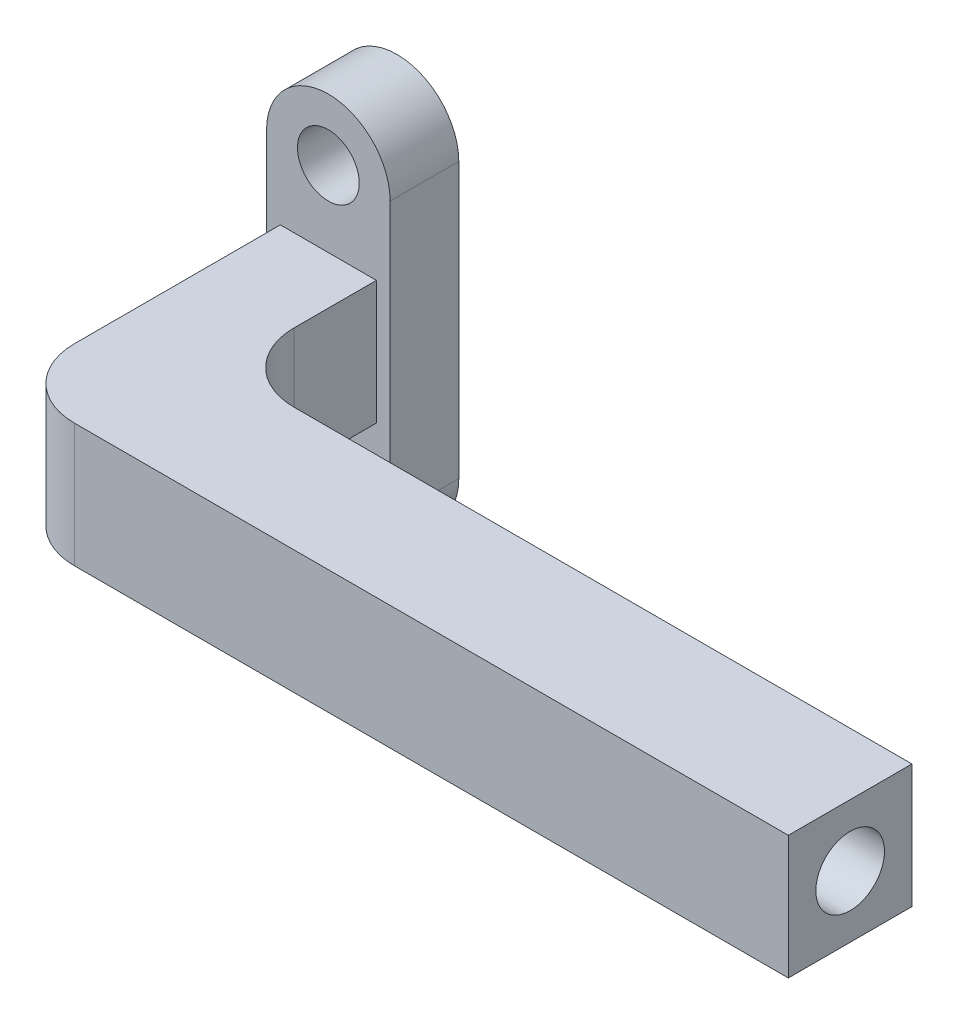
SolidWorks part; units mm, degrees
ref_plane "Front Plane" through (0, 0, 0) normal (0, 0, 1) x (1, 0, 0)
ref_plane "Top Plane" through (0, 0, 0) normal (0, 1, 0) x (1, 0, 0)
ref_plane "Right Plane" through (0, 0, 0) normal (1, 0, 0) x (0, 0, -1)
sketch "Sketch1" plane through (0, 0, 0) normal (0, 0, 1) x (1, 0, 0)
  line L0 (4.5, 10) -> (4.5, -10)
  line L1 (-4.5, 10) -> (-4.5, -10)
  circle A0 centre (0, 10) radius 2.25
  circle A1 centre (0, -10) radius 2.25
  circle A2 centre (0, 10) radius 4.5
  circle A3 centre (0, -10) radius 4.5
  dimension "D1" = 4.5
  dimension "D2" = 9
  dimension "D3" = 4.5
  dimension "D4" = 9
  dimension "D5" = 20
  dimension "D6" = 10
extrude "Boss-Extrude1" add sketch "Sketch1" along normal blind 5 contours A3 L0 A2 L1 | A3 A1 | A0
sketch "Sketch2" plane through (0, 0, 5) normal (0, 0, 1) x (1, 0, 0)
  line L1 (-3.5, -4.5) -> (3.5, -4.5)
  line L2 (-3.5, -4.5) -> (-3.5, 4.5)
  line L3 (-3.5, 4.5) -> (3.5, 4.5)
  line L4 (3.5, -4.5) -> (3.5, 4.5)
  line L5 (-3.5, -4.5) -> (3.5, 4.5) construction
  line L6 (-3.5, 4.5) -> (3.5, -4.5) construction
  point P0 (0, 0)
  dimension "D1" = 9
  dimension "D2" = 7
extrude "Boss-Extrude2" add sketch "Sketch2" along normal blind 20
sketch "Sketch4" plane through (3.5, 0, 0) normal (1, 0, 0) x (0, 0, -1)
  line L0 (-25, -4.5) -> (-5, -4.5) construction
  line L1 (-25, 4.5) -> (-16, 4.5)
  line L2 (-25, 4.5) -> (-25, -4.5)
  line L3 (-25, -4.5) -> (-16, -4.5)
  line L4 (-16, 4.5) -> (-16, -4.5)
  dimension "D1" = 9
extrude "Boss-Extrude4" add sketch "Sketch4" along normal blind 50
sketch "Sketch5" plane through (53.5, 0, 0) normal (1, 0, 0) x (0, 0, -1)
  circle A0 centre (-20.5, 0) radius 2.5
  dimension "D1" = 5
extrude "Cut-Extrude1" cut sketch "Sketch5" against normal blind 25
fillet "Fillet1" radius 5 1 edges at (3.5, 0, 16)
fillet "Fillet2" radius 5 1 edges at (-3.5, 0, 25)
